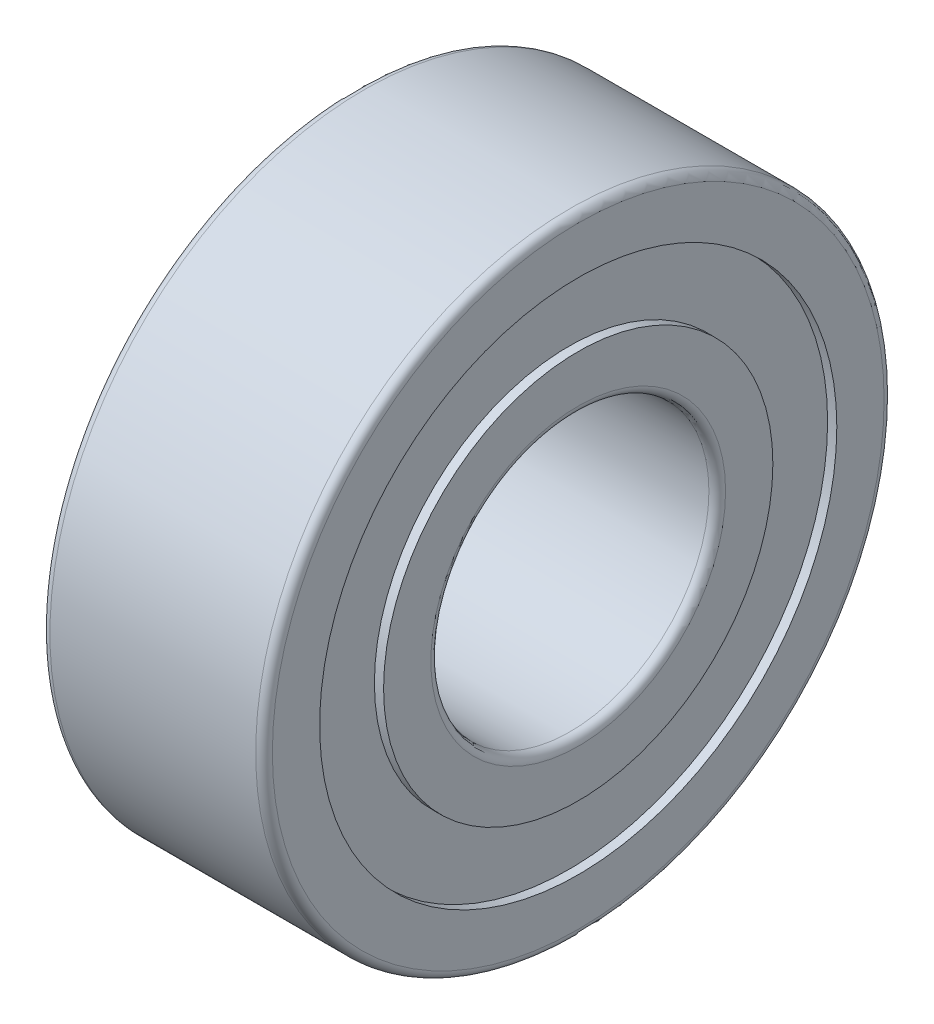
SolidWorks part; units mm, degrees
ref_plane "Front Plane" through (0, 0, 0) normal (0, 0, 1) x (1, 0, 0)
ref_plane "Top Plane" through (0, 0, 0) normal (0, 1, 0) x (1, 0, 0)
ref_plane "Right Plane" through (0, 0, 0) normal (1, 0, 0) x (0, 0, -1)
sketch "Sketch1" plane through (0, 0, 0) normal (0, 0, 1) x (1, 0, 0)
  line L0 (0, 3.5) -> (0, 2.65)
  line L1 (0.15, 2.5) -> (3.85, 2.5)
  line L2 (4, 2.65) -> (4, 3.5)
  line L3 (4, 3.5) -> (3.8345, 3.5)
  line L4 (3.8345, 3.5) -> (3.8345, 4.65)
  line L5 (3.8345, 4.65) -> (4, 4.65)
  line L6 (4, 4.65) -> (4, 5.5)
  line L7 (3.85, 5.65) -> (0.15, 5.65)
  line L8 (0, 5.5) -> (0, 4.65)
  line L9 (0, 4.65) -> (0.1655, 4.65)
  line L10 (0.1655, 4.65) -> (0.1655, 3.5)
  line L11 (0.1655, 3.5) -> (0, 3.5)
  line L12 (-0.0025, 0) -> (4.0025, 0) construction
  arc A0 (0, 2.65) -> (0.15, 2.5) centre (0.15, 2.65) ccw
  arc A1 (3.85, 2.5) -> (4, 2.65) centre (3.85, 2.65) ccw
  arc A2 (4, 5.5) -> (3.85, 5.65) centre (3.85, 5.5) ccw
  arc A3 (0.15, 5.65) -> (0, 5.5) centre (0.15, 5.5) ccw
  point P22 (2, 5.65)
  dimension "D1" = 2.5
  dimension "D2" = 5.65
  dimension "D3" = 1
  dimension "D4" = 1.15
  dimension "D5" = 4
revolve "Revolve1" add sketch "Sketch1" angle 360 about L12
